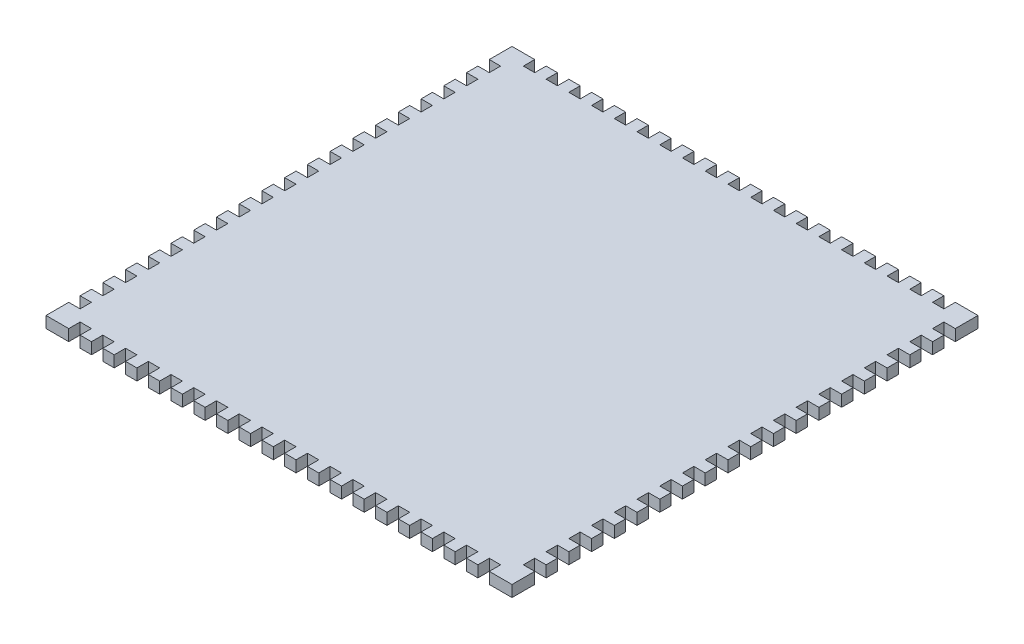
SolidWorks part; units mm, degrees
ref_plane "Front Plane" through (0, 0, 0) normal (0, 0, 1) x (1, 0, 0)
ref_plane "Top Plane" through (0, 0, 0) normal (0, 1, 0) x (1, 0, 0)
ref_plane "Right Plane" through (0, 0, 0) normal (1, 0, 0) x (0, 0, -1)
sketch "Sketch1" plane through (0, 0, 0) normal (0, 1, 0) x (1, 0, 0)
  line L1 (-130.175, -130.175) -> (130.175, -130.175)
  line L2 (-130.175, -130.175) -> (-130.175, 130.175)
  line L3 (-130.175, 130.175) -> (130.175, 130.175)
  line L4 (130.175, -130.175) -> (130.175, 130.175)
  line L5 (-130.175, -130.175) -> (130.175, 130.175) construction
  line L6 (-130.175, 130.175) -> (130.175, -130.175) construction
  point P0 (0, 0)
  dimension "D1" = 260.35
  dimension "D2" = 260.35
extrude "Boss-Extrude1" add sketch "Sketch1" along normal blind 6.35
sketch "Sketch2" plane through (0, 6.35, 0) normal (0, 1, 0) x (1, 0, 0)
  line L0 (130.175, 130.175) -> (-130.175, 130.175) construction
  line L1 (-117.475, 130.175) -> (-111.125, 130.175)
  line L2 (-117.475, 130.175) -> (-117.475, 123.825)
  line L3 (-117.475, 123.825) -> (-111.125, 123.825)
  line L4 (-111.125, 130.175) -> (-111.125, 123.825)
  dimension "D1" = 12.7
  dimension "D2" = 6.35
  dimension "D3" = 6.35
extrude "Cut-Extrude1" cut sketch "Sketch2" against normal through all
pattern_linear "LPattern1" count 19 spacing 12.7 along (1, 0, 0) of "Cut-Extrude1"
mirror "Mirror1" about plane through (0, 0, 0) normal (0, 0, 1) of "LPattern1", "Cut-Extrude1"
sketch "Sketch3" plane through (0, 6.35, 0) normal (0, 1, 0) x (1, 0, 0)
  line L0 (-130.175, 130.175) -> (-130.175, -130.175) construction
  line L1 (-130.175, 117.475) -> (-123.825, 117.475)
  line L2 (-130.175, 117.475) -> (-130.175, 111.125)
  line L3 (-130.175, 111.125) -> (-123.825, 111.125)
  line L4 (-123.825, 117.475) -> (-123.825, 111.125)
  dimension "D1" = 12.7
  dimension "D2" = 6.35
  dimension "D3" = 6.35
extrude "Cut-Extrude2" cut sketch "Sketch3" against normal through all
pattern_linear "LPattern2" count 19 spacing 12.7 along (0, 0, 1) of "Cut-Extrude2"
mirror "Mirror2" about plane through (0, 0, 0) normal (1, 0, 0) of "LPattern2", "Cut-Extrude2"
sketch "Sketch4" plane through (0, 6.35, 0) normal (0, 1, 0) x (1, 0, 0)
  line L1 (-130.175, 130.175) -> (-117.475, 130.175)
  line L2 (-130.175, 130.175) -> (-130.175, 123.825)
  line L3 (-130.175, 123.825) -> (-117.475, 123.825)
  line L4 (-117.475, 130.175) -> (-117.475, 123.825)
  dimension "D1" = 12.7
  dimension "D2" = 6.35
